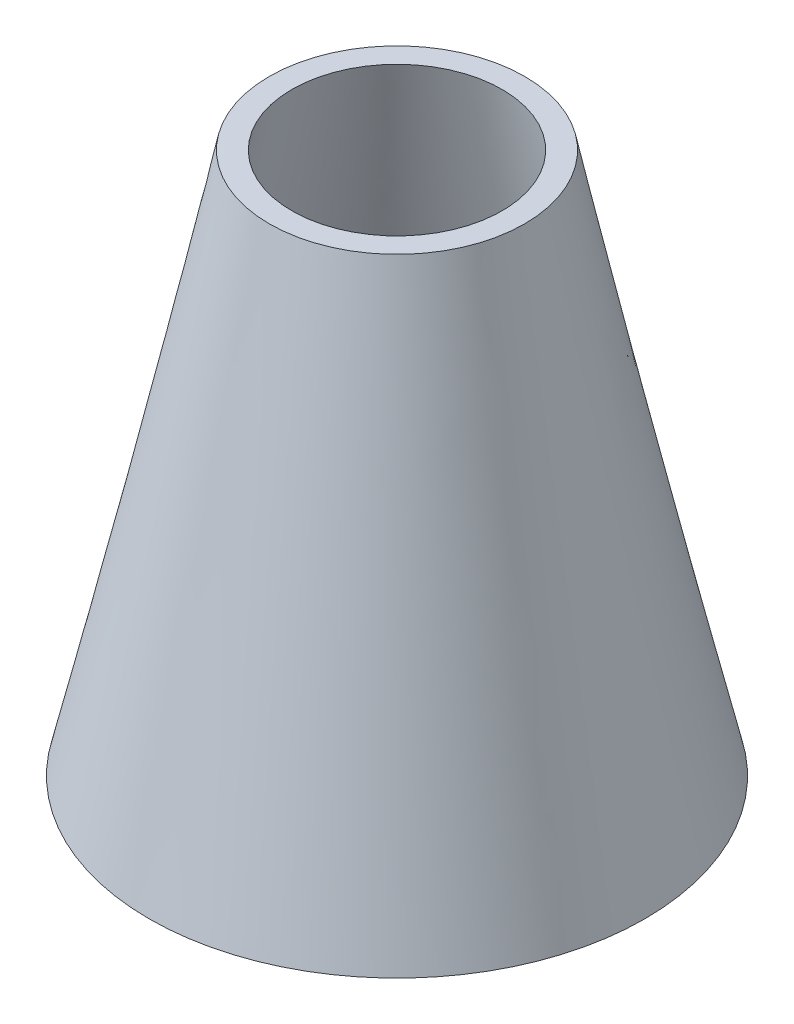
SolidWorks part; units mm, degrees
ref_plane "Front Plane" through (0, 0, 0) normal (0, 0, 1) x (1, 0, 0)
ref_plane "Top Plane" through (0, 0, 0) normal (0, 1, 0) x (1, 0, 0)
ref_plane "Right Plane" through (0, 0, 0) normal (1, 0, 0) x (0, 0, -1)
sketch "Sketch2" plane through (0, 0, 0) normal (0, 0, 1) x (1, 0, 0)
  line L0 (0, 105.448) -> (0, -81.5961) construction
  line L1 (35, 98.4039) -> (42.5, 98.4039)
  line L2 (74.9993, -81.9255) -> (82.4993, -81.9255)
  spline S0 degree 2 poles (35, 98.4039) (53.9092, 7.9967) (74.9993, -81.9255) knots 0 0 0 1 1 1
  spline S1 degree 2 poles (42.5, 98.4039) (61.4092, 7.9967) (82.4993, -81.9255) knots 0 0 0 1 1 1
  dimension "D2" = 7.5
  dimension "D1" = 35
  dimension "D3" = 75
  dimension "D4" = 180
  dimension "D5" = 7.5
  dimension "D6" = 7.5
  dimension "D7" = 180.3294
revolve "Revolve1" add sketch "Sketch2" angle 360 about L0
